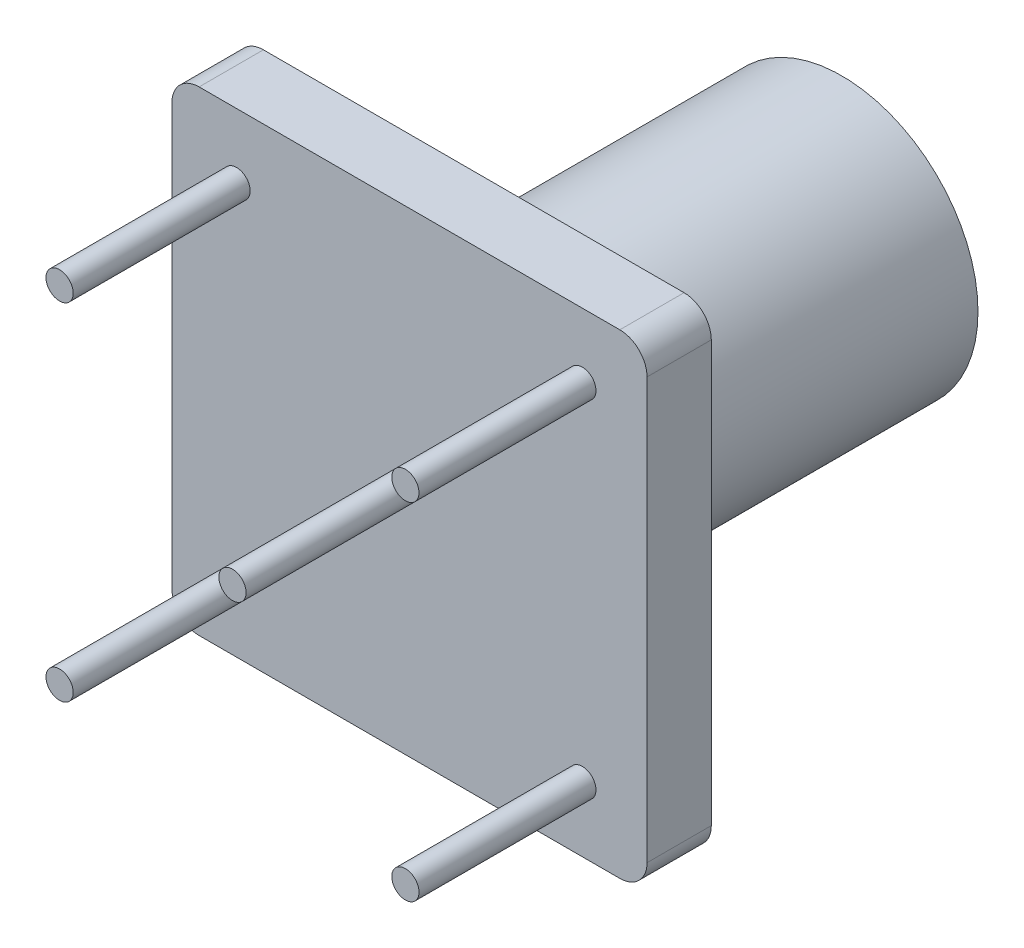
SolidWorks part; units mm, degrees
ref_plane "Front" through (0, 0, 0) normal (0, 0, 1) x (1, 0, 0)
ref_plane "Top" through (0, 0, 0) normal (0, 1, 0) x (1, 0, 0)
ref_plane "Right" through (0, 0, 0) normal (1, 0, 0) x (0, 0, -1)
sketch "Sketch1" plane through (0, 0, 0) normal (0, 0, 1) x (1, 0, 0)
  line L1 (1, 0) -> (16.45, 0)
  line L2 (0, -1) -> (0, -16.45)
  line L3 (1, -17.45) -> (16.45, -17.45)
  line L4 (17.45, -1) -> (17.45, -16.45)
  arc A0 (17.45, -1) -> (16.45, 0) centre (16.45, -1) ccw
  arc A1 (16.45, -17.45) -> (17.45, -16.45) centre (16.45, -16.45) ccw
  arc A2 (0, -16.45) -> (1, -17.45) centre (1, -16.45) ccw
  arc A3 (1, 0) -> (0, -1) centre (1, -1) ccw
  point P12 (0, 0)
  dimension "D3" = 1
  dimension "D1" = 17.45
  dimension "D2" = 17.45
extrude "Extrude1" add sketch "Sketch1" along normal blind 2.36
sketch "Sketch2" plane through (0, 0, 0) normal (0, 0, -1) x (-1, 0, 0)
  line L0 (0, -1) -> (0, -16.45) construction
  line L1 (-1, -17.45) -> (-16.45, -17.45) construction
  circle A0 centre (-8.725, -8.725) radius 5
  dimension "D1" = 10
  dimension "D2" = 8.725
  dimension "D3" = 8.725
extrude "Extrude2" add sketch "Sketch2" along normal blind 13.52
sketch "Sketch3" plane through (0, 0, -13.52) normal (0, 0, -1) x (-1, 0, 0)
  circle A0 centre (-8.725, -8.725) radius 4.5
  circle A1 centre (-8.725, -8.725) radius 5 construction
  dimension "D1" = 9
extrude "Cut-Extrude1" cut sketch "Sketch3" against normal blind 13.52
sketch "Sketch4" plane through (0, 0, 2.36) normal (0, 0, 1) x (1, 0, 0)
  line L0 (17.45, -16.45) -> (17.45, -1) construction
  line L1 (1, -17.45) -> (16.45, -17.45) construction
  circle A0 centre (8.725, -8.725) radius 0.5
  circle A1 centre (15.075, -2.375) radius 0.5
  circle A2 centre (2.375, -2.375) radius 0.5
  circle A3 centre (2.375, -15.075) radius 0.5
  circle A4 centre (15.075, -15.075) radius 0.5
  dimension "D1" = 1
  dimension "D4" = 1
  dimension "D5" = 1
  dimension "D6" = 1
  dimension "D7" = 1
  dimension "D2" = 8.725
  dimension "D3" = 8.725
  dimension "D8" = 6.35
  dimension "D9" = 6.35
  dimension "D10" = 6.35
  dimension "D11" = 6.35
extrude "Extrude3" add sketch "Sketch4" along normal blind 6.5
sketch "Sketch5" plane through (0, 0, 0) normal (0, 0, -1) x (-1, 0, 0)
  circle A0 centre (-8.725, -8.725) radius 0.5
  circle A1 centre (-8.725, -8.725) radius 4.5 construction
  dimension "D1" = 1
extrude "Extrude4" add sketch "Sketch5" along normal blind 9
